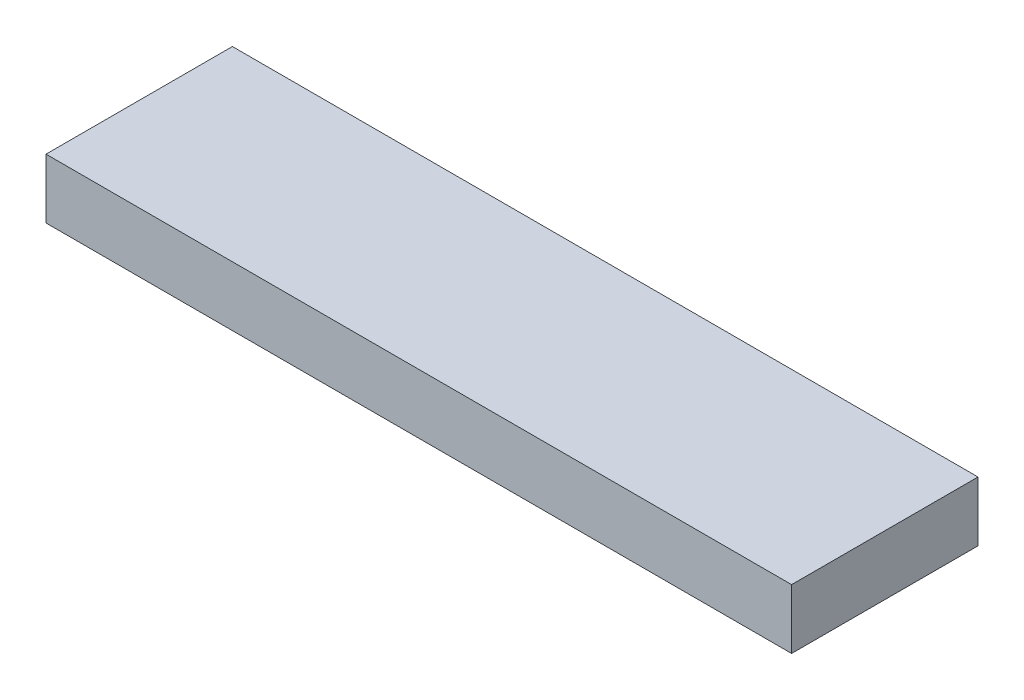
SolidWorks part; units mm, degrees
ref_plane "Plan de face" through (0, 0, 0) normal (0, 0, 1) x (1, 0, 0)
ref_plane "Plan de dessus" through (0, 0, 0) normal (0, 1, 0) x (1, 0, 0)
ref_plane "Plan de droite" through (0, 0, 0) normal (1, 0, 0) x (0, 0, -1)
sketch "Esquisse1" plane through (0, 0, 0) normal (0, 1, 0) x (1, 0, 0)
  line L1 (0, 0) -> (400, 0)
  line L2 (0, 0) -> (0, 100)
  line L3 (0, 100) -> (400, 100)
  line L4 (400, 0) -> (400, 100)
  dimension "D1" = 400
  dimension "D2" = 100
extrude "Extrusion1" add sketch "Esquisse1" along normal blind 32
